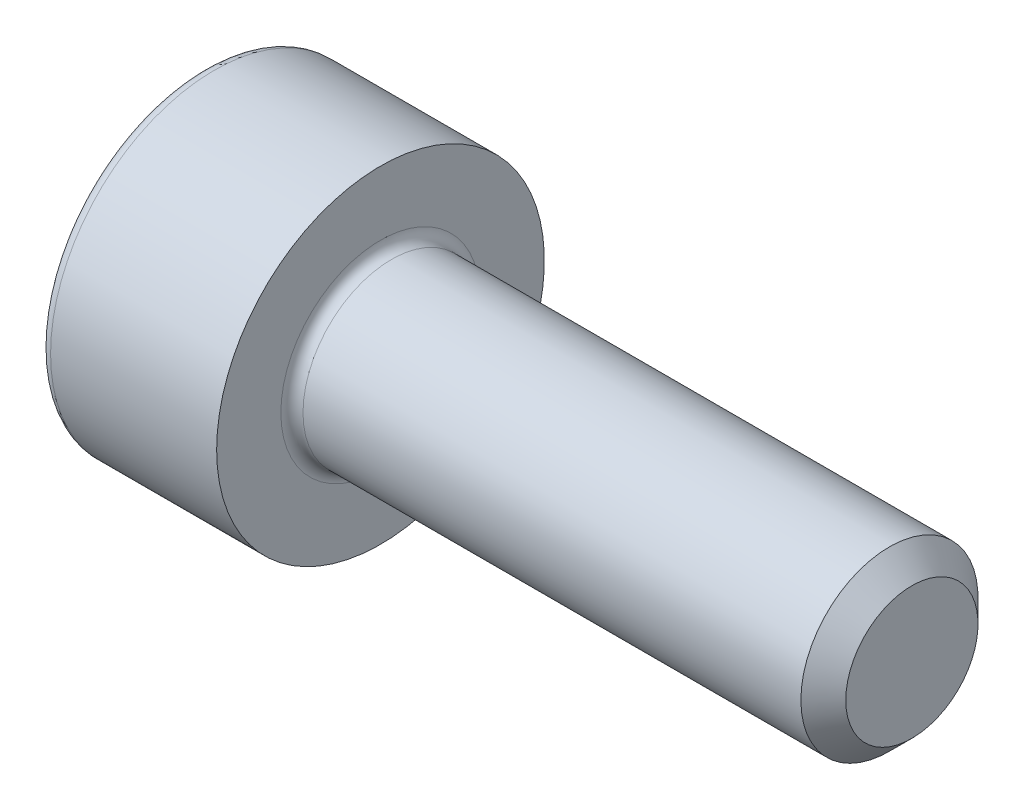
SolidWorks part; units mm, degrees
ref_plane "Front" through (0, 0, 0) normal (0, 0, 1) x (1, 0, 0)
ref_plane "Top" through (0, 0, 0) normal (0, 1, 0) x (1, 0, 0)
ref_plane "Right" through (0, 0, 0) normal (1, 0, 0) x (0, 0, -1)
sketch "Sketch1" plane through (0, 0, 0) normal (0, 0, 1) x (1, 0, 0)
  line L0 (5.7465, 1) -> (0.125, 1)
  line L1 (-2, 1.725) -> (-2, 0)
  line L2 (0, 1.85) -> (-1.875, 1.85)
  line L3 (0, 1.125) -> (0, 1.85)
  line L4 (6, 0.7465) -> (6, 0)
  line L5 (6, 0.7465) -> (5.7465, 1)
  line L6 (-2, 0) -> (0, 0) construction
  line L7 (-2, 0) -> (6, 0)
  arc A0 (-1.875, 1.85) -> (-2, 1.725) centre (-1.875, 1.725) ccw
  arc A1 (0, 1.125) -> (0.125, 1) centre (0.125, 1.125) ccw
  point P12 (0, 1.4875)
  dimension "D5" = 0.125
  dimension "D1" = 2
  dimension "D2" = 3.7
  dimension "D3" = 135
  dimension "D4" = 0.3585
  dimension "D6" = 6
  dimension "D7" = 2
revolve "Revolve1" add sketch "Sketch1" angle 360 about L7
sketch "Sketch2" plane through (-2, 0, 0) normal (-1, 0, 0) x (0, 0, 1)
  line L7 (0.75, 0.433) -> (0, 0.866)
  line L8 (0, 0.866) -> (-0.75, 0.433)
  line L9 (-0.75, 0.433) -> (-0.75, -0.433)
  line L10 (-0.75, -0.433) -> (0, -0.866)
  line L11 (0, -0.866) -> (0.75, -0.433)
  line L12 (0.75, -0.433) -> (0.75, 0.433)
  circle A0 centre (0, 0) radius 0.75 construction
  dimension "D1" = 1.5
extrude "Cut-Extrude1" cut sketch "Sketch2" against normal blind 1.1
